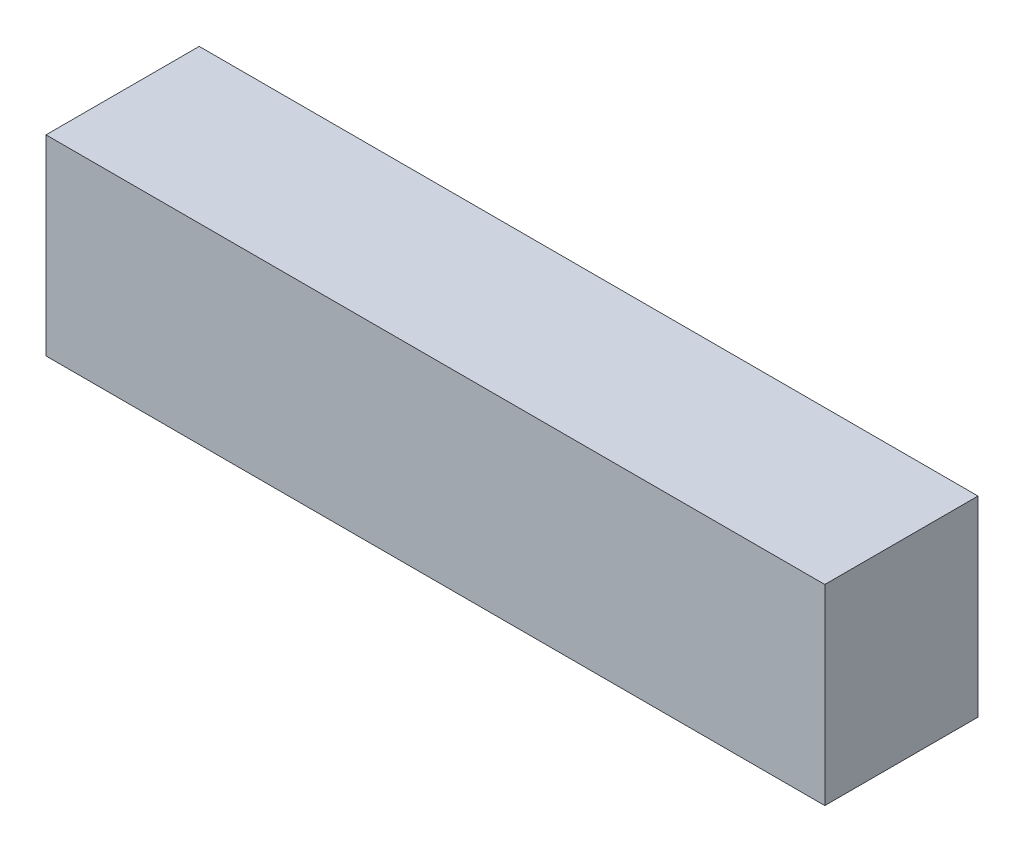
SolidWorks part; units mm, degrees
ref_plane "Front Plane" through (0, 0, 0) normal (0, 0, 1) x (1, 0, 0)
ref_plane "Top Plane" through (0, 0, 0) normal (0, 1, 0) x (1, 0, 0)
ref_plane "Right Plane" through (0, 0, 0) normal (1, 0, 0) x (0, 0, -1)
sketch "Sketch1" plane through (0, 0, 0) normal (0, 0, 1) x (1, 0, 0)
  line L1 (0, 0) -> (61, 0)
  line L2 (0, 0) -> (0, -15)
  line L3 (0, -15) -> (61, -15)
  line L4 (61, 0) -> (61, -15)
  dimension "D1" = 61
  dimension "D2" = 15
extrude "Boss-Extrude1" add sketch "Sketch1" along normal blind 12
